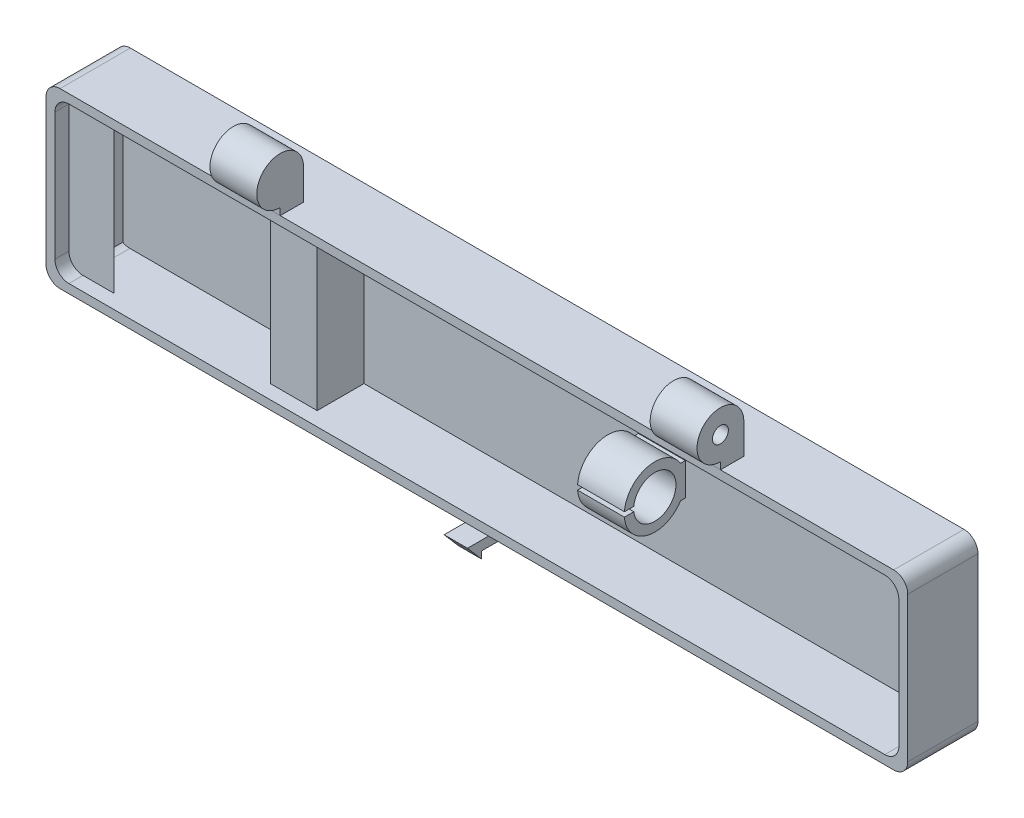
SolidWorks part; units mm, degrees
ref_plane "Alzado" through (0, 0, 0) normal (0, 0, 1) x (1, 0, 0)
ref_plane "Planta" through (0, 0, 0) normal (0, 1, 0) x (1, 0, 0)
ref_plane "Vista lateral" through (0, 0, 0) normal (1, 0, 0) x (0, 0, -1)
sketch "Croquis1" plane through (0, 0, 0) normal (0, 0, 1) x (1, 0, 0)
  line L1 (0, 0) -> (-184, 0)
  line L2 (0, 0) -> (0, 37)
  line L3 (0, 37) -> (-184, 37)
  line L4 (-184, 0) -> (-184, 37)
  dimension "D1" = 184
  dimension "D2" = 37
extrude "Saliente-Extruir1" add sketch "Croquis1" along normal blind 15
sketch "Croquis3" plane through (0, 0, 15) normal (0, 0, 1) x (1, 0, 0)
  line L8 (-1.9, 1.9) -> (-1.9, 35.1)
  line L9 (-1.9, 35.1) -> (-182.1, 35.1)
  line L10 (-182.1, 35.1) -> (-182.1, 1.9)
  line L11 (-182.1, 1.9) -> (-1.9, 1.9)
  line L12 (-1.9, 1.9) -> (-1.9, 35.1)
  line L13 (-1.9, 35.1) -> (-182.1, 35.1)
  line L14 (-182.1, 35.1) -> (-182.1, 1.9)
  line L15 (-182.1, 1.9) -> (-1.9, 1.9)
  dimension "D1" = 1.9
extrude "Cortar-Extruir2" cut sketch "Croquis3" against normal blind 13
sketch "Croquis4" plane through (-184, 0, 0) normal (-1, 0, 0) x (0, 0, 1)
  line L0 (15, 38.5) -> (15, 37)
  line L1 (15, 37) -> (15, 0) construction
  line L3 (10, 43.5) -> (10, 37)
  line L4 (15, 37) -> (0, 37) construction
  line L5 (15, 37) -> (10, 37)
  circle A0 centre (15, 43.5) radius 1.7 construction
  circle A1 centre (15, 43.5) radius 3 construction
  arc A2 (15, 38.5) -> (10, 43.5) centre (15, 43.5) ccw
  dimension "D1" = 3.4
  dimension "D2" = 10
  dimension "D3" = 6
  dimension "D4" = 1.5
extrude "Saliente-Extruir2" add sketch "Croquis4" against normal blind 10 from offset 40 separate body offset against normal yes
ref_plane "Plano1" through (-92, 0, 0) normal (-1, 0, 0) x (0, 0, 1)
sketch "Croquis5" plane through (-144, 0, 0) normal (-1, 0, 0) x (0, 0, 1)
  circle A0 centre (15, 43.5) radius 1.7
  dimension "D1" = 3.4
extrude "Cortar-Extruir3" cut sketch "Croquis5" against normal blind 5
mirror "Simetría1" about plane through (-92, 0, 0) normal (-1, 0, 0) of bodies 108 105 104
fillet "Redondeo1" radius 3 8 edges at (-1.9, 1.9, 8.5) (-1.9, 35.1, 8.5) (-182.1, 1.9, 8.5) (-182.1, 35.1, 8.5) (0, 37, 7.5) (0, 0, 7.5) (-184, 37, 7.5) (-184, 0, 7.5)
sketch "Croquis6" plane through (-184, 0, 0) normal (-1, 0, 0) x (0, 0, 1)
  line L0 (15, 0) -> (19.5, 0)
  line L1 (19.5, 0) -> (19.5, -3.5) construction
  line L2 (19.5, -3.5) -> (16.5, -3.5) construction
  line L3 (16.5, -3.5) -> (16.5, -2) construction
  line L4 (19.5, 0) -> (16.5, -3.5)
  line L5 (16.5, -3.5) -> (16.5, -2)
  line L6 (16.5, -2) -> (10, -2)
  line L7 (10, -2) -> (7.6667, 0)
  line L8 (15, 0) -> (0, 0) construction
  line L9 (7.6667, 0) -> (15, 0)
  dimension "D1" = 4.5
  dimension "D2" = 3.5
  dimension "D3" = 3
  dimension "D4" = 1.5
extrude "Saliente-Extruir3" add sketch "Croquis6" along normal blind 2.5 and the other way blind 2.5 from surface at -92 starting at plane "Plano1"
sketch "Croquis7" plane through (-1.9, 0, 0) normal (-1, 0, 0) x (0, 0, 1)
  line L0 (2, 32.1) -> (2, 4.9) construction
  line L1 (15, 4.9) -> (15, 32.1) construction
  line L2 (3, 21.9669) -> (2, 21.9669)
  line L3 (2, 21.9669) -> (2, 18.5)
  line L4 (3, 15.0331) -> (2, 15.0331)
  line L5 (2, 15.0331) -> (2, 18.5)
  line L6 (15, 19) -> (15, 18) construction
  line L8 (15, 19) -> (13, 19)
  line L9 (15, 18) -> (13, 18)
  arc A0 (13, 19) -> (13, 18) centre (8.5096, 18.5) ccw
  arc A1 (3, 15.0331) -> (15, 18) centre (8.5096, 18.5) ccw
  arc A2 (15, 19) -> (3, 21.9669) centre (8.5096, 18.5) ccw
  point P8 (15, 18.5)
  dimension "D1" = 2
  dimension "D3" = 1
  dimension "D4" = 1
extrude "Saliente-Extruir4" add sketch "Croquis7" along normal blind 5 and the other way blind 5 from offset 63.6
sketch "Croquis8" plane through (0, 35.1, 0) normal (0, -1, 0) x (1, 0, 0)
  line L0 (-179.1, 2) -> (-129.1, 2) construction
  line L1 (-4.9, 2) -> (-179.1, 2) construction
  line L2 (-129.1, 2) -> (-129.1, 12)
  line L4 (-129.1, 12) -> (-139.1, 12)
  line L5 (-139.1, 12) -> (-131, 3.9)
  line L6 (-131, 3.9) -> (-131, 2)
  line L7 (-131, 2) -> (-129.1, 2)
  line L8 (-182.5, 12) -> (-172.5, 12)
  line L10 (-172.5, 12) -> (-180.6, 3.9)
  line L11 (-180.6, 3.9) -> (-180.6, 2)
  line L12 (-180.6, 2) -> (-182.5, 2)
  line L14 (-182.5, 2) -> (-182.5, 12)
  dimension "D1" = 50
  dimension "D2" = 10
  dimension "D3" = 45
  dimension "D4" = 45
  dimension "D5" = 1.9
  dimension "D6" = 1.9
  dimension "D7" = 10
  dimension "D8" = 10
  dimension "D9" = 10
extrude "Saliente-Extruir5" add sketch "Croquis8" along normal up to surface (33.2 mm away) up to face at (-92, 1.9, 8.5)
